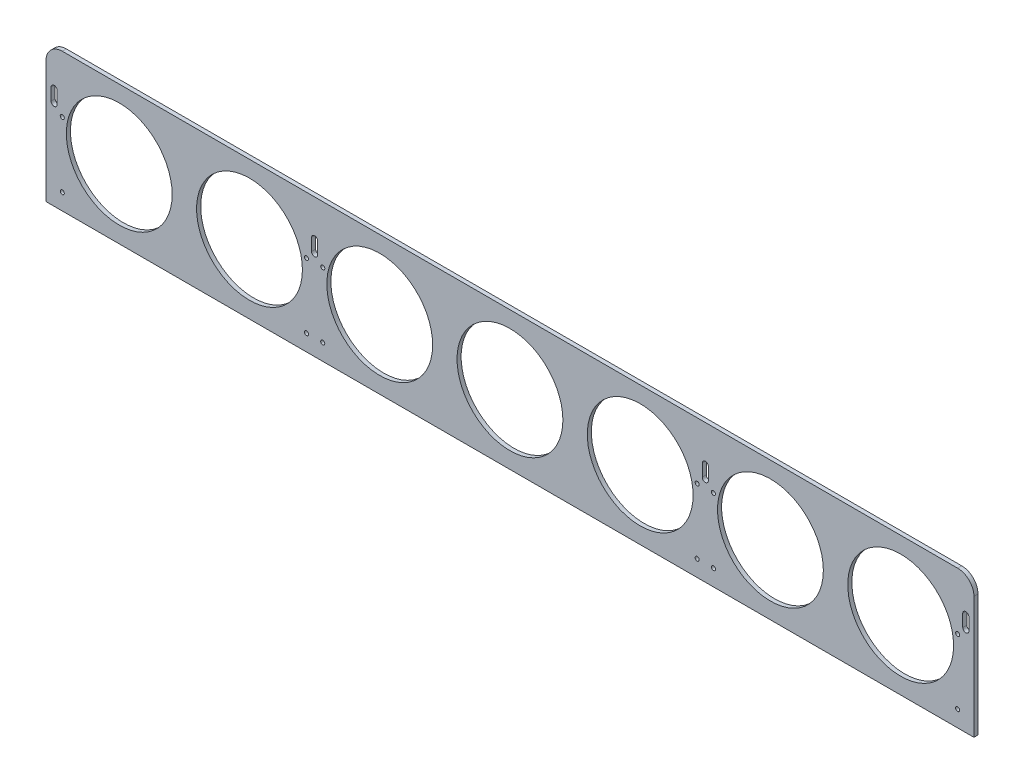
SolidWorks part; units mm, degrees
material "PC High Viscosity"
ref_plane "Front Plane" through (0, 0, 0) normal (0, 0, 1) x (1, 0, 0)
ref_plane "Top Plane" through (0, 0, 0) normal (0, 1, 0) x (1, 0, 0)
ref_plane "Right Plane" through (0, 0, 0) normal (1, 0, 0) x (0, 0, -1)
sketch "Sketch1" plane through (0, 0, 0) normal (0, 0, 1) x (1, 0, 0)
  line L1 (723.9, 107.95) -> (-723.9, 107.95)
  line L2 (723.9, 107.95) -> (723.9, -107.95)
  line L3 (723.9, -107.95) -> (-723.9, -107.95)
  line L4 (-723.9, 107.95) -> (-723.9, -107.95)
  line L5 (723.9, 107.95) -> (-723.9, -107.95) construction
  line L6 (723.9, -107.95) -> (-723.9, 107.95) construction
  point P0 (0, 0)
  dimension "D1" = 1447.8
  dimension "D2" = 215.9
extrude "Boss-Extrude1" add sketch "Sketch1" along normal blind 6.35
sketch "Sketch2" plane through (0, 0, 6.35) normal (0, 0, 1) x (1, 0, 0)
  line L1 (-723.9, -107.95) -> (723.9, -107.95) construction
  line L2 (-723.9, 107.95) -> (-723.9, -107.95) construction
  circle A0 centre (-609.6, 0) radius 82.55
  dimension "D1" = 107.95
  dimension "D2" = 165.1
  dimension "D3" = 114.3
extrude "Cut-Extrude1" cut sketch "Sketch2" against normal through all
pattern_linear "LPattern1" count 7 spacing 203.2 along (1, 0, 0) of "Cut-Extrude1"
fillet "Fillet1" radius 25.4 2 edges at (723.9, 107.95, 3.175) (-723.9, 107.95, 3.175)
sketch "Sketch3" plane through (0, 0, 6.35) normal (0, 0, 1) x (1, 0, 0)
  line L0 (-711.2, 50.8) -> (-711.2, 31.75) construction
  line L1 (-706.4375, 50.8) -> (-706.4375, 31.75)
  line L2 (-715.9625, 50.8) -> (-715.9625, 31.75)
  line L3 (-723.9, -107.95) -> (723.9, -107.95) construction
  arc A0 (-706.4375, 50.8) -> (-715.9625, 50.8) centre (-711.2, 50.8) ccw
  arc A1 (-715.9625, 31.75) -> (-706.4375, 31.75) centre (-711.2, 31.75) ccw
  point P2 (-711.2, 41.275)
  dimension "D1" = 9.525
  dimension "D2" = 19.05
  dimension "D3" = 711.2
  dimension "D4" = 158.75
extrude "Cut-Extrude2" cut sketch "Sketch3" against normal through all
pattern_linear "LPattern2" count 2 spacing 406.4 along (1, 0, 0) of "Cut-Extrude2"
mirror "Mirror1" about plane through (0, 0, 0) normal (1, 0, 0) of "LPattern2", "Cut-Extrude2"
sketch "Sketch4" plane through (0, 0, 6.35) normal (0, 0, 1) x (1, 0, 0)
  line L0 (-723.9, 82.55) -> (-723.9, -107.95) construction
  line L1 (-723.9, -107.95) -> (723.9, -107.95) construction
  circle A0 centre (-698.5, 19.05) radius 3.175
  circle A1 centre (-317.5, 19.05) radius 3.175
  circle A2 centre (-292.1, 19.05) radius 3.175
  circle A5 centre (-698.5, -82.55) radius 3.175
  circle A6 centre (-317.5, -82.55) radius 3.175
  circle A7 centre (-292.1, -82.55) radius 3.175
  dimension "D1" = 6.35
  dimension "D6" = 25.4
  dimension "D2" = 25.4
  dimension "D3" = 127
  dimension "D4" = 317.5
  dimension "D5" = 292.1
extrude "Cut-Extrude3" cut sketch "Sketch4" against normal through all
mirror "Mirror2" about plane through (0, 0, 0) normal (1, 0, 0) of "Cut-Extrude3"
